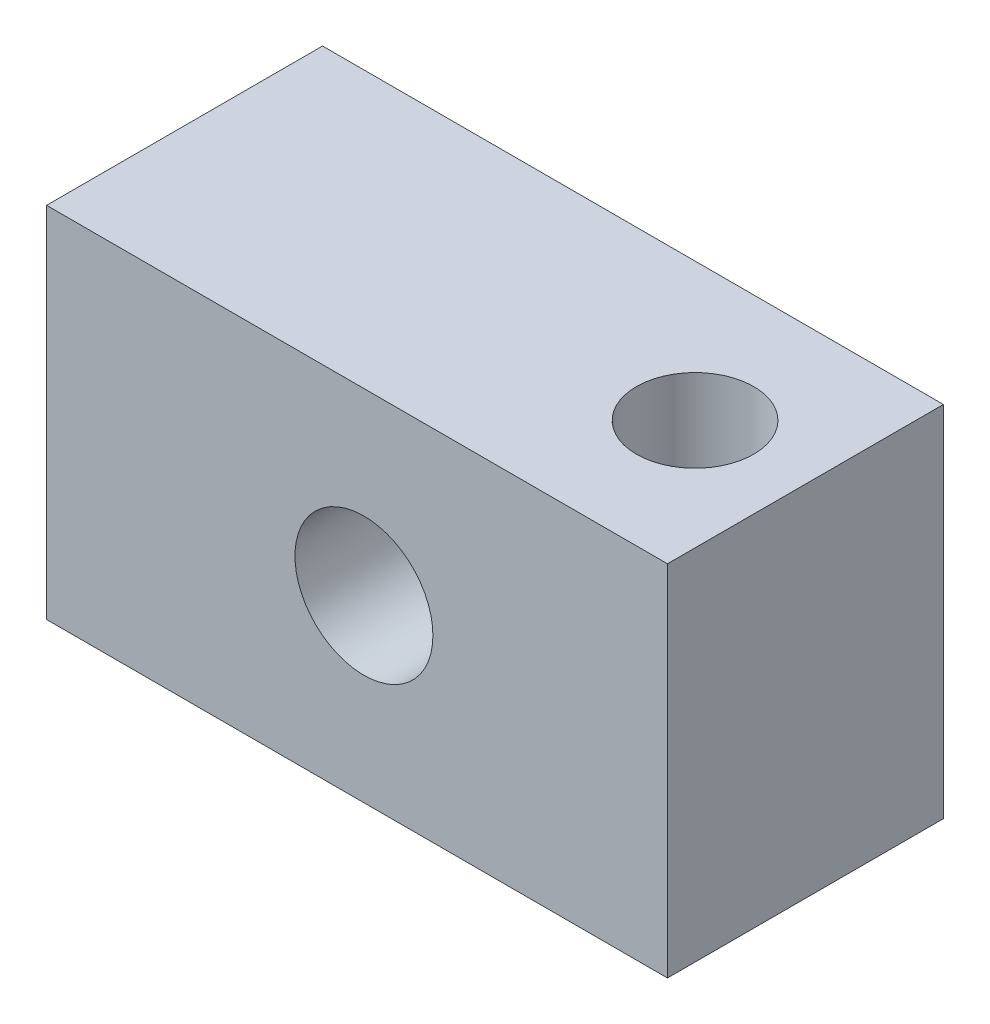
SolidWorks part; units mm, degrees
ref_plane "Plan de face" through (0, 0, 0) normal (0, 0, 1) x (1, 0, 0)
ref_plane "Plan de dessus" through (0, 0, 0) normal (0, 1, 0) x (1, 0, 0)
ref_plane "Plan de droite" through (0, 0, 0) normal (1, 0, 0) x (0, 0, -1)
sketch "Esquisse1" plane through (0, 0, 0) normal (0, 0, 1) x (1, 0, 0)
  line L1 (-45, 26) -> (0, 26)
  line L2 (-45, 26) -> (-45, 0)
  line L3 (-45, 0) -> (0, 0)
  line L4 (0, 26) -> (0, 0)
  dimension "D1" = 26
  dimension "D2" = 45
extrude "Boss.-Extru.1" add sketch "Esquisse1" along normal blind 20
sketch "Esquisse3" plane through (0, 0, 0) normal (0, 0, -1) x (-1, 0, 0)
  line L0 (0, 0) -> (0, 26) construction
  circle A0 centre (22, 13) radius 5
  dimension "D1" = 22
extrude "Enlèv. mat.-Extru.1" cut sketch "Esquisse3" against normal up to next and the other way through all
hole_wizard "Trou taraudé M101" positions "Esquisse4" profile "Esquisse5" tap size "M10" standard "ISO" end condition up to next
sketch "Esquisse4" plane through (0, 26, 0) normal (0, 1, 0) x (1, 0, 0)
  line L1 (0, -20) -> (-45, -20) construction
  line L2 (0, -20) -> (0, 0) construction
  point P0 (-8, -10)
  dimension "D1" = 10
  dimension "D2" = 8
sketch "Esquisse5" plane through (-8, 26, 10) normal (1, 0, 0) x (0, 0, 1)
  line L0 (0, 0) -> (0, 26)
  line L1 (0, 26) -> (4.25, 26)
  line L2 (4.25, 26) -> (4.25, 0)
  line L5 (4.25, 0) -> (0, 0)
  line L11 (0, -6.35) -> (0, 107.95) construction
  dimension "Diamètre du trou pour taraudage jusqu'au prochain" = 8.5
  dimension "Profondeur du trou pour taraudage jusqu'au prochain" = 26
cosmetic thread "Filetage de perçage1" parameters "D2"=10
